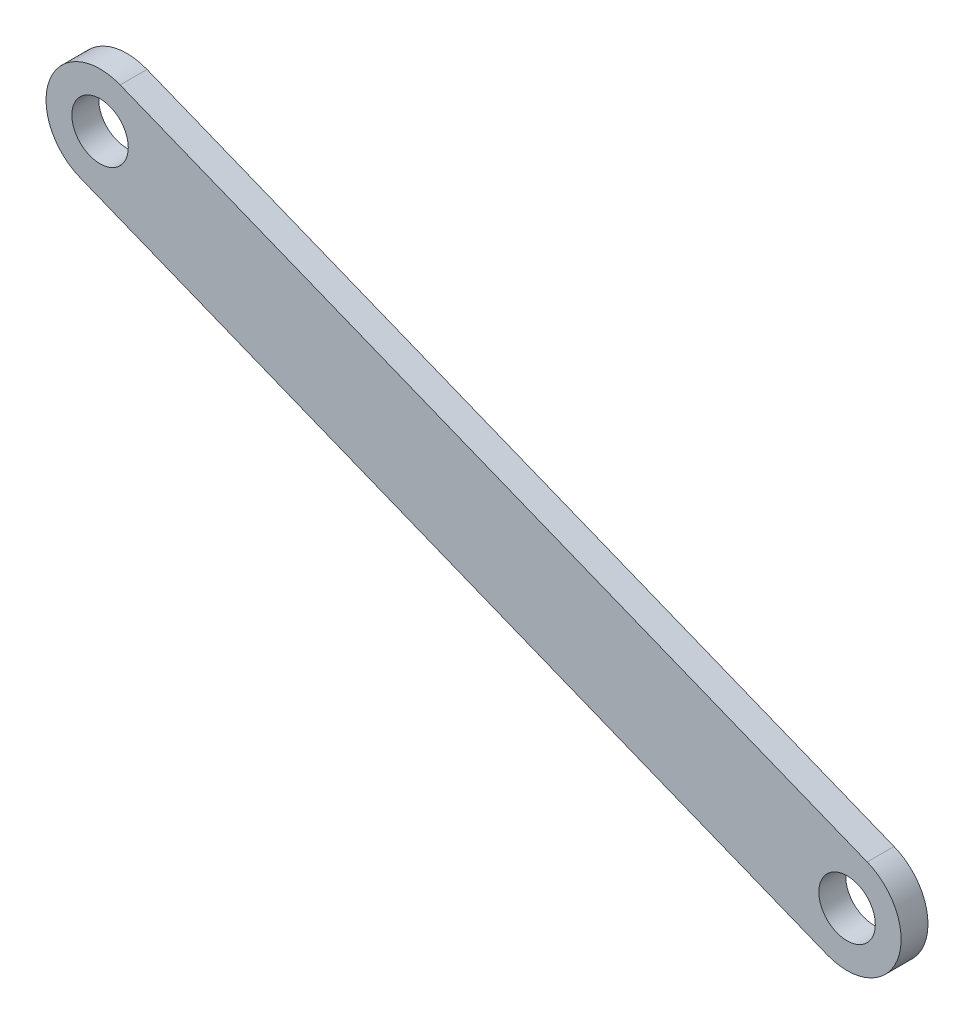
SolidWorks part; units mm, degrees
ref_plane "Front Plane" through (0, 0, 0) normal (0, 0, 1) x (1, 0, 0)
ref_plane "Top Plane" through (0, 0, 0) normal (0, 1, 0) x (1, 0, 0)
ref_plane "Right Plane" through (0, 0, 0) normal (1, 0, 0) x (0, 0, -1)
sketch "Sketch2" plane through (0, 0, 0) normal (0, 0, 1) x (1, 0, 0)
  line L0 (-245.0363, -22.4425) -> (-133.8307, -67.0135) construction
  line L1 (-242.0447, -14.9784) -> (-130.8391, -59.5495)
  line L2 (-248.0279, -29.9065) -> (-136.8222, -74.4775)
  arc A0 (-242.0447, -14.9784) -> (-248.0279, -29.9065) centre (-245.0363, -22.4425) ccw
  arc A1 (-136.8222, -74.4775) -> (-130.8391, -59.5495) centre (-133.8307, -67.0135) ccw
  point P2 (-189.4335, -44.728)
extrude "Boss-Extrude1" add sketch "Sketch2" along normal blind 4
hole_wizard "M8 Clearance Hole1" positions "Sketch3" profile "Sketch4" hole size "M8" standard "ISO" end condition through all
sketch "Sketch3" plane through (0, 0, 4) normal (0, 0, 1) x (1, 0, 0)
  circle A0 centre (-245.0363, -22.4425) radius 4
  circle A1 centre (-133.8307, -67.0135) radius 4
  circle A2 centre (-133.8307, -67.0135) radius 4
  circle A3 centre (-245.0363, -22.4425) radius 4
  point P0 (-245.0363, -22.4425)
  point P2 (-133.8307, -67.0135)
sketch "Sketch4" plane through (-245.0363, -22.4425, 4) normal (1, 0, 0) x (0, -1, 0)
  line L0 (0, 0) -> (0, 4)
  line L1 (0, 4) -> (4.2, 4)
  line L2 (4.2, 4) -> (4.2, 0)
  line L5 (4.2, 0) -> (0, 0)
  line L11 (0, -6.35) -> (0, 107.95) construction
  dimension "Thru Hole Dia." = 8.4
  dimension "Thru Hole Depth" = 4
